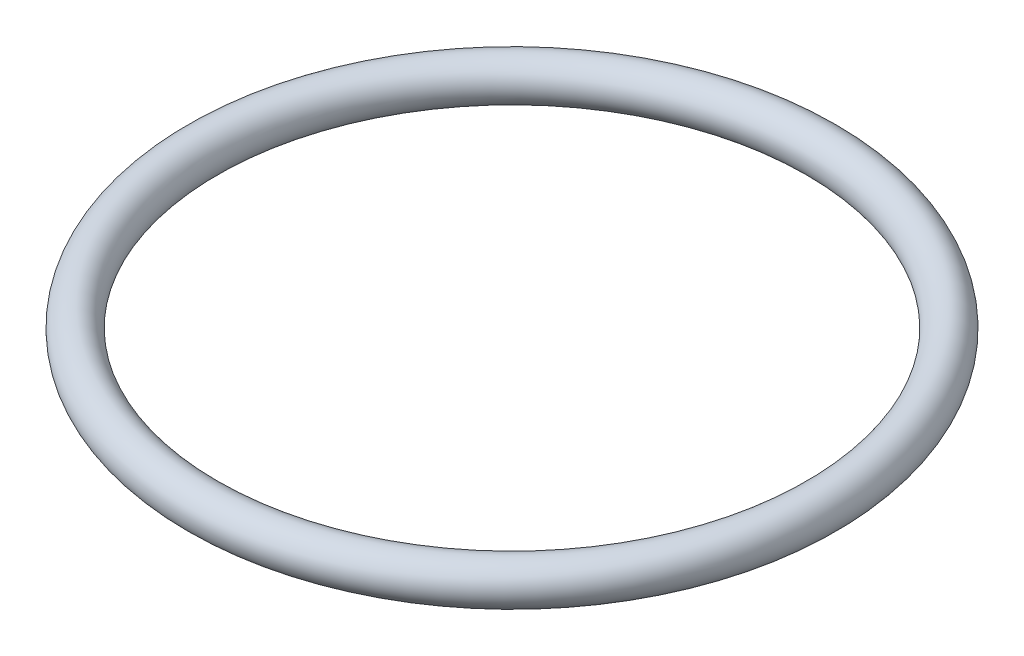
SolidWorks part; units mm, degrees
material "POLYURETHANE (11671)"
ref_plane "Front Plane" through (0, 0, 0) normal (0, 0, 1) x (1, 0, 0)
ref_plane "Top Plane" through (0, 0, 0) normal (0, 1, 0) x (1, 0, 0)
ref_plane "Right Plane" through (0, 0, 0) normal (1, 0, 0) x (0, 0, -1)
sketch "Sketch1" plane through (0, 0, 0) normal (0, 0, 1) x (1, 0, 0)
  line L0 (0, 6.9783) -> (0, -3.0879) construction
  circle A0 centre (11.25, 0) radius 0.75
  dimension "D1" = 1.5
  dimension "D2" = 11.25
  dimension "D3" = 0
revolve "Revolve1" add sketch "Sketch1" angle 360 about L0
sketch "Sketch2" plane through (0, 0, 0) normal (0, 1, 0) x (1, 0, 0)
  circle A0 centre (0, 0) radius 12 construction
